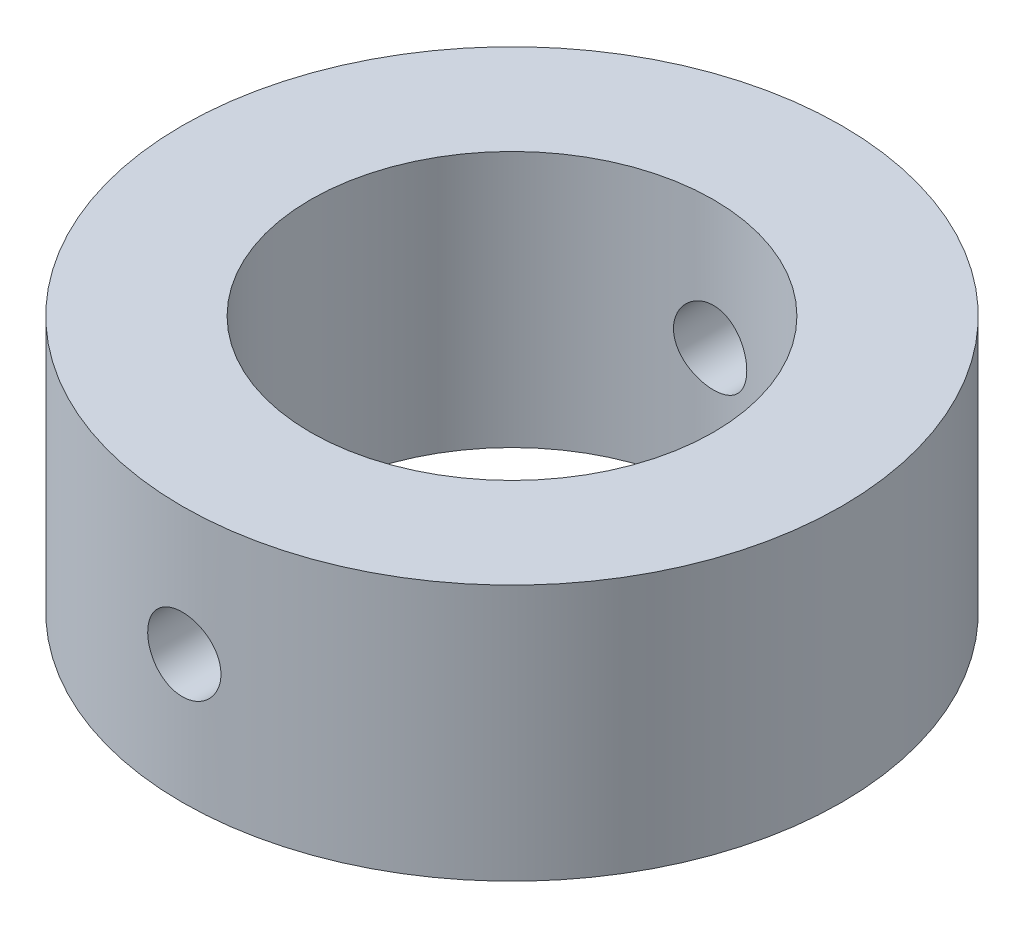
SolidWorks part; units mm, degrees
ref_plane "Front Plane" through (0, 0, 0) normal (0, 0, 1) x (1, 0, 0)
ref_plane "Top Plane" through (0, 0, 0) normal (0, 1, 0) x (1, 0, 0)
ref_plane "Right Plane" through (0, 0, 0) normal (1, 0, 0) x (0, 0, -1)
sketch "Sketch1" plane through (0, 0, 0) normal (0, 0, 1) x (1, 0, 0)
  line L0 (-15.5436, 0) -> (13.1744, 0) construction
  line L1 (0, 17.5538) -> (0, -18.2) construction
  line L3 (11, 7) -> (18, 7)
  line L4 (11, 7) -> (11, -7)
  line L5 (11, -7) -> (18, -7)
  line L6 (18, 7) -> (18, -7)
  line L7 (11, 7) -> (18, -7) construction
  line L8 (11, -7) -> (18, 7) construction
  point P5 (14.5, 0)
  dimension "D1" = 14
  dimension "D2" = 18
  dimension "D3" = 11
revolve "Revolve1" add sketch "Sketch1" angle 360 about L1
sketch "Sketch2" plane through (0, 0, 0) normal (0, 0, 1) x (1, 0, 0)
  circle A0 centre (0, 0) radius 2
  dimension "D1" = 4
extrude "Cut-Extrude1" cut sketch "Sketch2" against normal mid plane 66
